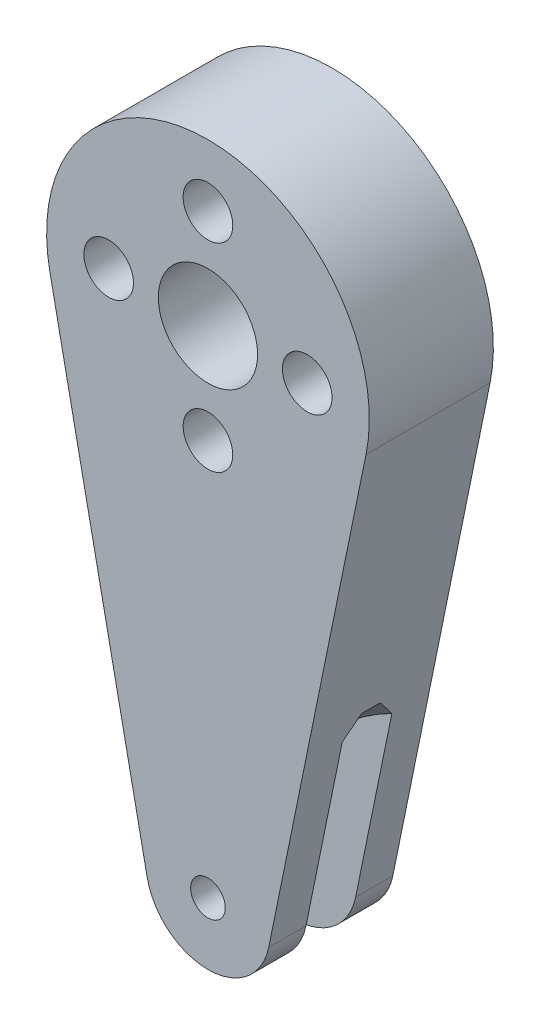
SolidWorks part; units mm, degrees
ref_plane "Front" through (0, 0, 0) normal (0, 0, 1) x (1, 0, 0)
ref_plane "Top" through (0, 0, 0) normal (0, 1, 0) x (1, 0, 0)
ref_plane "Right" through (0, 0, 0) normal (1, 0, 0) x (0, 0, -1)
sketch "Sketch1" plane through (0, 0, 0) normal (0, 0, 1) x (1, 0, 0)
  line L0 (4.8986, -40.9243) -> (12.7363, -2.6051)
  line L1 (-4.8986, -40.9243) -> (-12.7363, -2.6051)
  line L2 (32, -32) -> (16.975, -32) construction
  line L3 (32, -32) -> (17.487, -35.8888) construction
  circle A0 centre (0, 0) radius 4
  circle A1 centre (0, -32) radius 4 construction
  circle A2 centre (32, -32) radius 4 construction
  circle A3 centre (32, -32) radius 15.025 construction
  circle A4 centre (0, -24) radius 1.5 construction
  circle A5 centre (8, -32) radius 1.5 construction
  circle A6 centre (0, -40) radius 1.5 construction
  circle A7 centre (-8, -32) radius 1.5 construction
  circle A8 centre (0, 0) radius 39.9224 construction
  circle A9 centre (0, 8) radius 2
  circle A10 centre (8, 0) radius 2
  circle A11 centre (0, -8) radius 2
  circle A12 centre (-8, 0) radius 2
  circle A13 centre (0, -39.9224) radius 1.395
  arc A14 (4.8986, -40.9243) -> (-4.8986, -40.9243) centre (0, -39.9224) cw
  arc A15 (-12.7363, -2.6051) -> (12.7363, -2.6051) centre (0, 0) cw
  point P19 (0, -32)
  point P29 (0, 0)
  point P31 (17.487, -35.8888)
  dimension "D3" = 8
  dimension "D4" = 30.05
  dimension "D6" = 3
  dimension "D9" = 4
  dimension "D11" = 2.79
  dimension "D12" = 5
  dimension "D13" = 3
  dimension "D1" = 32
  dimension "D2" = 32
  dimension "D5" = 8
  dimension "D8" = 8
  dimension "D14" = 15
  dimension "D7" = 4
  dimension "D10" = 4
extrude "Boss-Extrude1" add sketch "Sketch1" along normal mid plane 10
sketch "Sketch2" plane through (0, 0, 0) normal (0, 0, 1) x (1, 0, 0)
  circle A0 centre (0, -39.9224) radius 5
  arc A1 (-4.8986, -40.9243) -> (4.8986, -40.9243) centre (0, -39.9224) ccw construction
extrude "Boss-Extrude2" add sketch "Sketch2" along normal mid plane 4 separate body
combine bodies "Combine1" operation type subtract main body 101 bodies to subtract 102
sketch "Sketch3" plane through (0, 0, 0) normal (0, 0, 1) x (1, 0, 0)
  line L6 (0, -40) -> (14.0109, -46.4117) construction
  line L7 (14.0109, -46.4117) -> (15.8048, -42.4917) construction
  line L8 (0, -40) -> (15.8048, -42.4917) construction
  line L9 (14.0109, -46.4117) -> (14.0109, -42.1007) construction
  circle A0 centre (15.8048, -42.4917) radius 19
  dimension "D1" = 38
  dimension "D2" = 16
  dimension "D3" = 4.311
  dimension "D4" = 24.59
extrude "Boss-Extrude3" add sketch "Sketch3" along normal up to surface and the other way up to surface separate body up to face at (1.395, -39.9224, 2) other way up to face at (1.395, -39.9224, -2)
chamfer "Chamfer1" distance 1.25 angle 45 2 edges at (34.8048, -42.4917, -2) (34.8048, -42.4917, 2)
combine bodies "Combine2" operation type subtract main body 103 bodies to subtract 104
